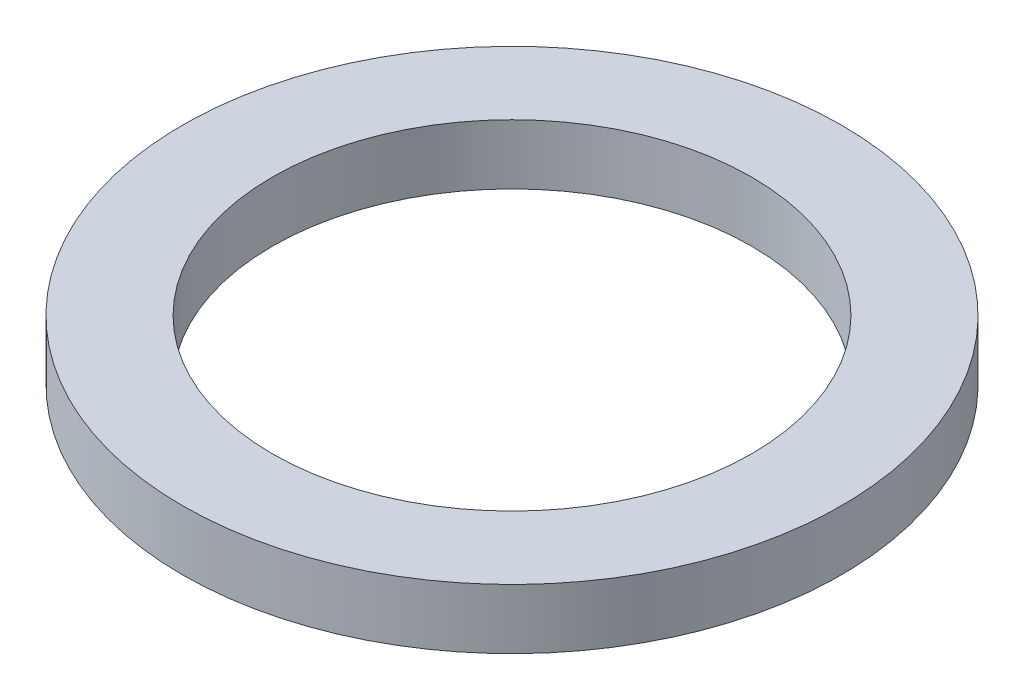
SolidWorks part; units mm, degrees
material "Cast Alloy Steel"
ref_plane "Front Plane" through (0, 0, 0) normal (0, 0, 1) x (1, 0, 0)
ref_plane "Top Plane" through (0, 0, 0) normal (0, 1, 0) x (1, 0, 0)
ref_plane "Right Plane" through (0, 0, 0) normal (1, 0, 0) x (0, 0, -1)
sketch "Sketch1" plane through (0, 0, 0) normal (0, 1, 0) x (1, 0, 0)
  circle A0 centre (0, 0) radius 4
  circle A1 centre (0, 0) radius 5.5
  dimension "D1" = 8
  dimension "D2" = 1.5
extrude "Boss-Extrude1" add sketch "Sketch1" along normal mid plane 1
